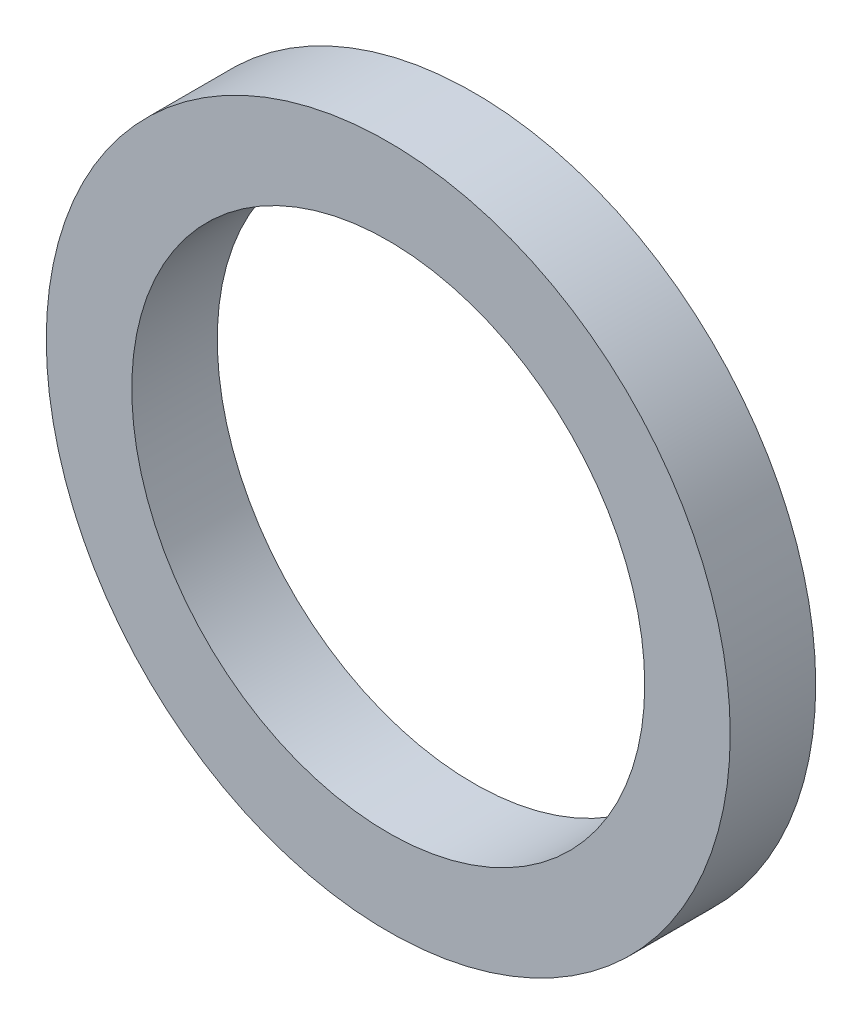
SolidWorks part; units mm, degrees
ref_plane "Front Plane" through (0, 0, 0) normal (0, 0, 1) x (1, 0, 0)
ref_plane "Top Plane" through (0, 0, 0) normal (0, 1, 0) x (1, 0, 0)
ref_plane "Right Plane" through (0, 0, 0) normal (1, 0, 0) x (0, 0, -1)
sketch "Sketch1" plane through (0, 0, 0) normal (0, 0, 1) x (1, 0, 0)
  circle A0 centre (0, 0) radius 12.7
  circle A1 centre (0, 0) radius 9.525
  dimension "D1" = 19.05
  dimension "D2" = 25.4
extrude "Boss-Extrude1" add sketch "Sketch1" along normal blind 3.175
